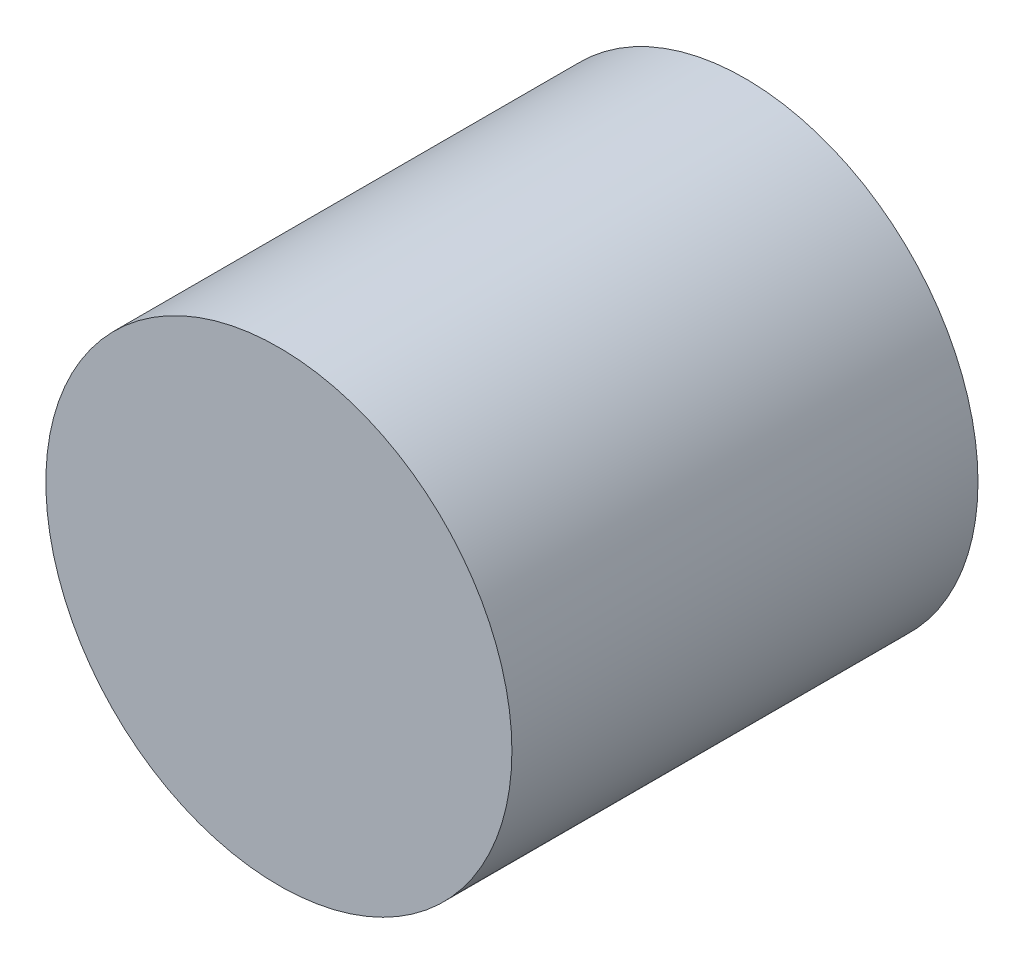
SolidWorks part; units mm, degrees
ref_plane "Piano frontale" through (0, 0, 0) normal (0, 0, 1) x (1, 0, 0)
ref_plane "Piano superiore" through (0, 0, 0) normal (0, 1, 0) x (1, 0, 0)
ref_plane "Piano destro" through (0, 0, 0) normal (1, 0, 0) x (0, 0, -1)
sketch "Schizzo1" plane through (0, 0, 0) normal (0, 0, 1) x (1, 0, 0)
  circle A0 centre (0, 0) radius 0.5
  dimension "D1" = 1
extrude "Estrusione-Estrusione1" add sketch "Schizzo1" along normal mid plane 1
